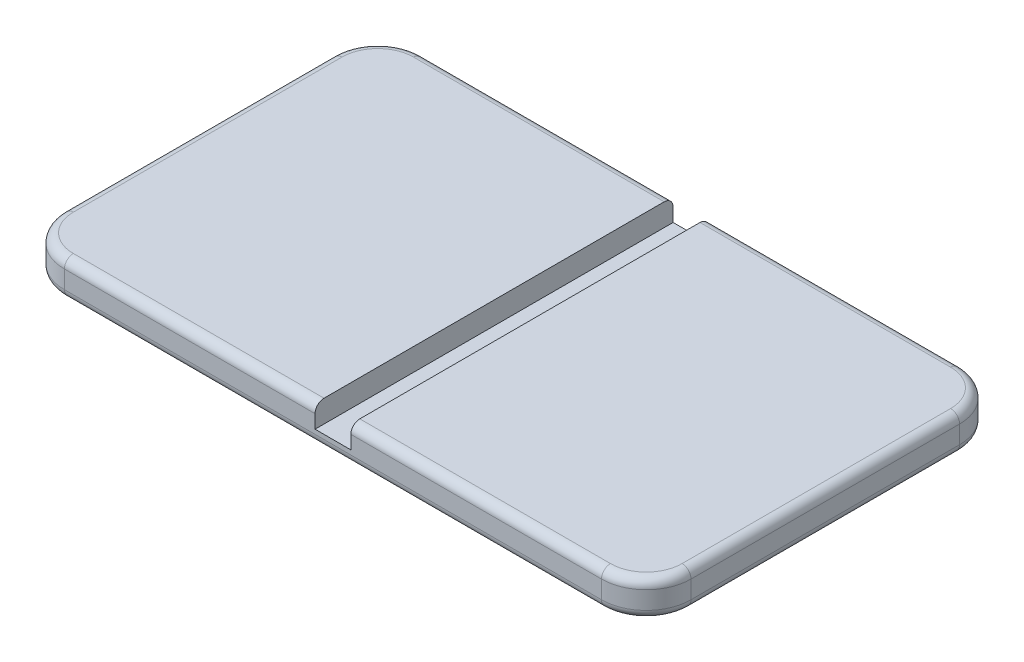
SolidWorks part; units mm, degrees
ref_plane "Přední rovina" through (0, 0, 0) normal (0, 0, 1) x (1, 0, 0)
ref_plane "Vrchní rovina" through (0, 0, 0) normal (0, 1, 0) x (1, 0, 0)
ref_plane "Pravá rovina" through (0, 0, 0) normal (1, 0, 0) x (0, 0, -1)
sketch "Skica1" plane through (0, 0, 0) normal (0, 1, 0) x (1, 0, 0)
  line L1 (0, 0) -> (140, 0)
  line L2 (0, 0) -> (0, 80)
  line L3 (0, 80) -> (140, 80)
  line L4 (140, 0) -> (140, 80)
  dimension "D1" = 140
  dimension "D2" = 80
extrude "Přidat vysunutím1" add sketch "Skica1" along normal blind 8
sketch "Skica2" plane through (0, 0, 0) normal (0, 0, 1) x (1, 0, 0)
  line L1 (66, 8) -> (74, 8)
  line L2 (66, 8) -> (66, 3)
  line L3 (66, 3) -> (74, 3)
  line L4 (74, 8) -> (74, 3)
  line L5 (0, 8) -> (140, 8) construction
  point P6 (70, 8)
  point P7 (70, 8)
  dimension "D1" = 5
  dimension "D2" = 8
extrude "Odebrat vysunutím1" cut sketch "Skica2" against normal up to next
fillet "Zaoblit1" radius 10 4 edges at (0, 4, -80) (140, 4, -80) (140, 4, 0) (0, 4, 0)
fillet "Zaoblit3" radius 2 18 edges at (2.9289, 0, -2.9289) (70, 0, 0) (137.0711, 0, -2.9289) (140, 0, -40) (137.0711, 0, -77.0711) (70, 0, -80) (2.9289, 0, -77.0711) (0, 0, -40) (137.0711, 8, -2.9289) (102, 8, 0) (102, 8, -80) (137.0711, 8, -77.0711) (140, 8, -40) (38, 8, 0) (2.9289, 8, -2.9289) (0, 8, -40) (2.9289, 8, -77.0711) (38, 8, -80)
